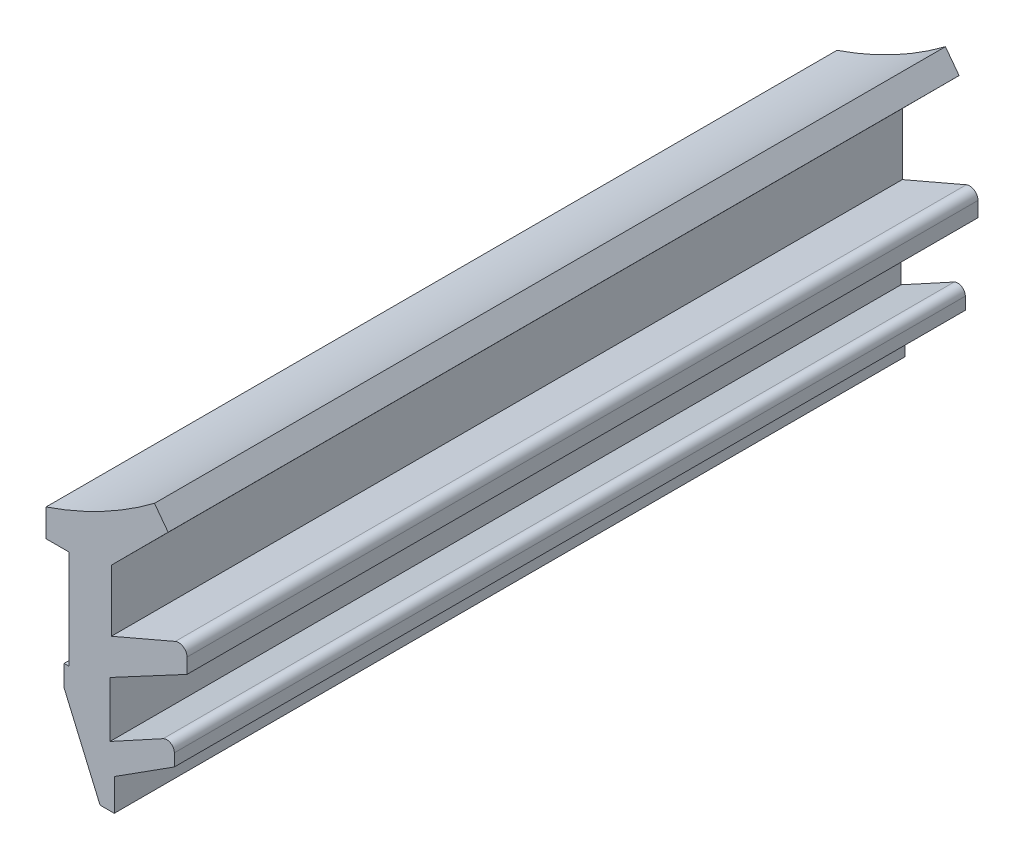
SolidWorks part; units mm, degrees
ref_plane "Спереди" through (0, 0, 0) normal (0, 0, 1) x (1, 0, 0)
ref_plane "Сверху" through (0, 0, 0) normal (0, 1, 0) x (1, 0, 0)
ref_plane "Справа" through (0, 0, 0) normal (1, 0, 0) x (0, 0, -1)
sketch "Эскиз1" plane through (0, 0, 0) normal (0, 0, 1) x (1, 0, 0)
  line L0 (7.4318, 45.0734) -> (67.5749, 45.0734) construction
  line L1 (0, 0) -> (0, -5)
  line L2 (0, 0) -> (-1.1523, 0)
  line L3 (-1.1523, 0) -> (-1.1523, 1.3917)
  line L4 (4.3336, 4.2944) -> (5.0248, 3.3736)
  line L5 (5.0248, 3.3736) -> (2.1542, 0.4979)
  line L6 (2.1542, 0.4979) -> (2.1542, -2.6169)
  line L7 (2.1542, -2.6169) -> (5.387, -1.2266)
  line L8 (5.9801, -1.6172) -> (5.9801, -2.3742)
  line L9 (5.9801, -2.3742) -> (2.0855, -4.4565)
  line L10 (2.0855, -4.4565) -> (2.0855, -7.2586)
  line L11 (2.0855, -7.2586) -> (4.7721, -5.7937)
  line L12 (5.3387, -6.1301) -> (5.3387, -6.7494)
  line L13 (5.3387, -6.7494) -> (2.2999, -8.6882)
  line L14 (2.2999, -8.6882) -> (2.2999, -10.3)
  line L15 (2.2999, -10.3) -> (1.5809, -10.3)
  line L16 (1.5809, -10.3) -> (-0.2351, -6.0775)
  line L17 (-0.2351, -6.0775) -> (-0.2351, -5)
  line L18 (-0.2351, -5) -> (0, -5)
  arc A0 (-1.1523, 1.3917) -> (4.3336, 4.2944) centre (-7.5611, 20.1396) ccw
  arc A1 (5.387, -1.2266) -> (5.9801, -1.6172) centre (5.5549, -1.6172) cw
  arc A2 (4.7721, -5.7937) -> (5.3387, -6.1301) centre (4.9555, -6.1301) cw
  dimension "D1" = 5
extrude "Бобышка-Вытянуть1" add sketch "Эскиз1" along normal blind 40
